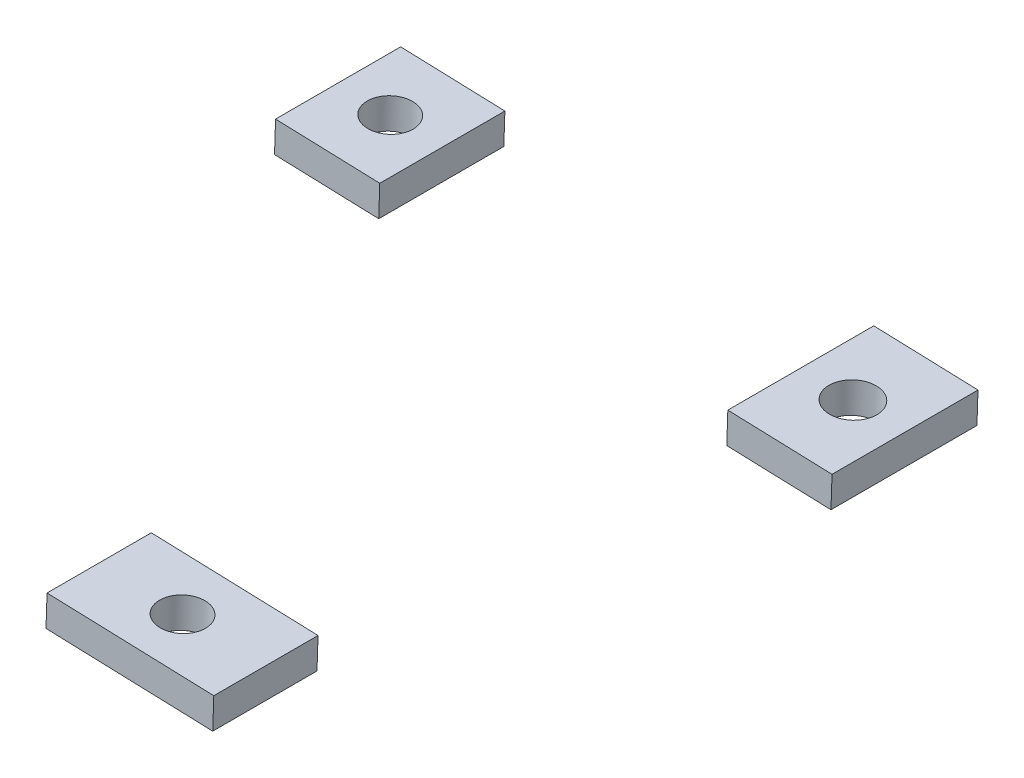
SolidWorks part; units mm, degrees
ref_plane "Front Plane" through (0, 0, 0) normal (0, 0, 1) x (1, 0, 0)
ref_plane "Top Plane" through (0, 0, 0) normal (0, 1, 0) x (1, 0, 0)
ref_plane "Right Plane" through (0, 0, 0) normal (1, 0, 0) x (0, 0, -1)
sketch "Sketch1" plane through (0.1623, 4.8513, 0) normal (0.0334, 0.9994, 0) x (0.9994, -0.0334, 0)
  line L1 (-116.1362, -115.9089) -> (-108.1362, -115.9089)
  line L2 (-116.1362, -115.9089) -> (-116.1362, -120.9089)
  line L3 (-116.1362, -120.9089) -> (-108.1362, -120.9089)
  line L4 (-108.1362, -115.9089) -> (-108.1362, -120.9089)
  line L5 (-107.6862, -96.7089) -> (-102.6862, -96.7089)
  line L6 (-107.6862, -96.7089) -> (-107.6862, -89.7089)
  line L7 (-107.6862, -89.7089) -> (-102.6862, -89.7089)
  line L8 (-102.6862, -96.7089) -> (-102.6862, -89.7089)
  line L9 (-129.8862, -90.2089) -> (-124.8862, -90.2089)
  line L10 (-129.8862, -90.2089) -> (-129.8862, -96.2089)
  line L11 (-129.8862, -96.2089) -> (-124.8862, -96.2089)
  line L12 (-124.8862, -90.2089) -> (-124.8862, -96.2089)
  circle A3 centre (-105.1862, -93.2089) radius 1.15
  circle A4 centre (-112.1362, -118.4089) radius 1.1
  circle A5 centre (-127.3862, -93.2089) radius 1.1
  point P1 (0, 0)
  point P3 (-146.535, -130.6146)
  point P5 (-132.0423, -102.0776)
  point P21 (0, 0)
  point P22 (-124.8862, -90.2089)
  dimension "D13" = 2.2
  dimension "D14" = 2.3
  dimension "D15" = 2.2
  dimension "D1" = 3
  dimension "D2" = 3
  dimension "D3" = 2.5
  dimension "D4" = 2.5
  dimension "D5" = 2.5
  dimension "D6" = 2.5
  dimension "D7" = 3.5
  dimension "D8" = 3.5
  dimension "D9" = 2.5
  dimension "D10" = 2.5
  dimension "D11" = 4
  dimension "D12" = 4
  dimension "D16" = 25.2
  dimension "D17" = 22.2
  dimension "D18" = 25.2
  dimension "D19" = 15.25
extrude "Boss-Extrude1" add sketch "Sketch1" along normal blind 1.5
